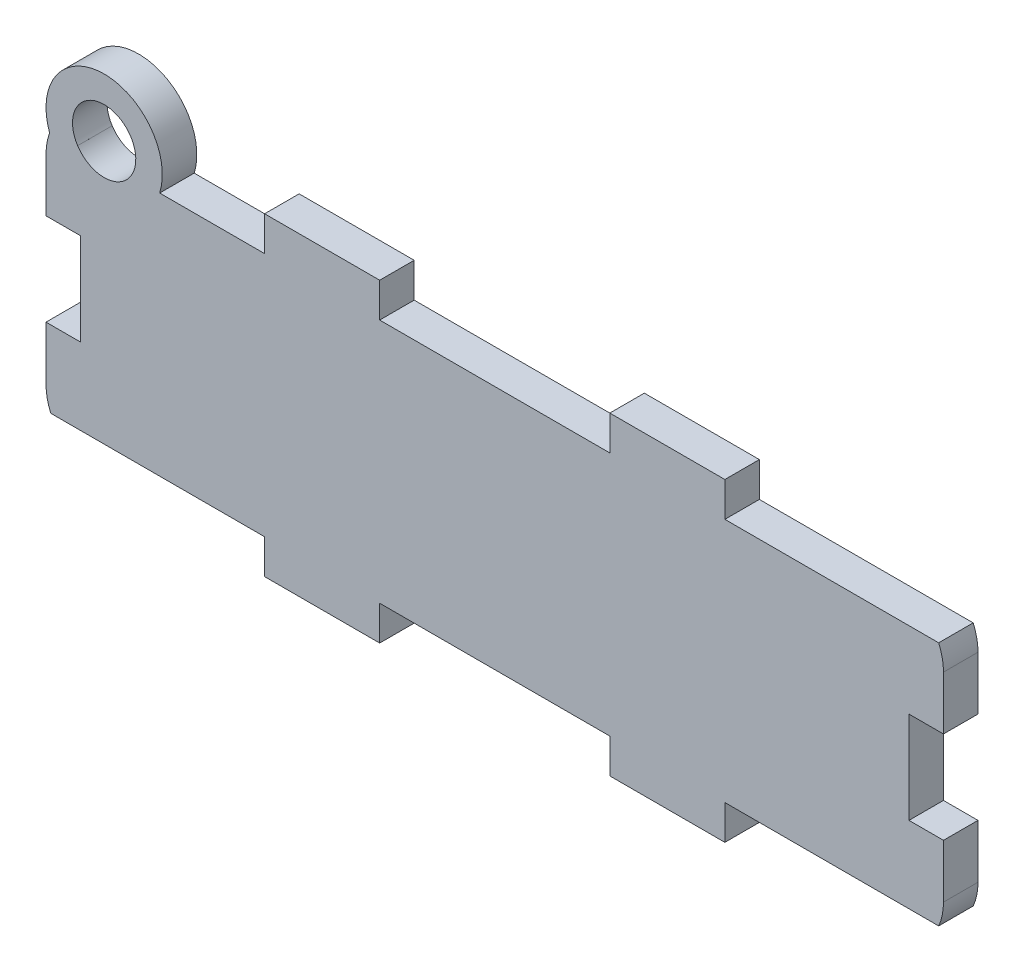
SolidWorks part; units mm, degrees
ref_plane "Front Plane" through (0, 0, 0) normal (0, 0, 1) x (1, 0, 0)
ref_plane "Top Plane" through (0, 0, 0) normal (0, 1, 0) x (1, 0, 0)
ref_plane "Right Plane" through (0, 0, 0) normal (1, 0, 0) x (0, 0, -1)
sketch "Sketch1" plane through (0, 0, 0) normal (0, 0, 1) x (1, 0, 0)
  line L0 (52, -3) -> (52, 0) construction
  line L1 (-7, -3) -> (3, -3)
  line L2 (-26, 2) -> (-26, 19.3118)
  line L3 (-7, 24.3118) -> (3, 24.3118)
  line L4 (52, 2) -> (52, 19.3118)
  line L5 (-26, -3) -> (52, 24.3118) construction
  line L6 (-26, 24.3118) -> (52, -3) construction
  line L7 (23, -3) -> (33, -3)
  line L8 (-7, 0) -> (-25.5826, 0)
  line L9 (-7, 0) -> (-7, -3)
  line L12 (-7, 0) -> (-26, -3) construction
  line L13 (-7, -3) -> (-26, 0) construction
  line L15 (3, -3) -> (3, 0)
  line L16 (3, 0) -> (23, 0)
  line L17 (23, -3) -> (23, 0)
  line L18 (3, -3) -> (23, 0) construction
  line L19 (3, 0) -> (23, -3) construction
  line L21 (33, -3) -> (33, 0)
  line L22 (33, 0) -> (51.5826, 0)
  line L24 (33, -3) -> (52, 0) construction
  line L25 (33, 0) -> (52, -3) construction
  line L27 (-33.6771, 10.6559) -> (59.6771, 10.6559) construction
  line L28 (33, 24.3118) -> (33, 21.3118)
  line L29 (23, 24.3118) -> (33, 24.3118)
  line L30 (23, 24.3118) -> (23, 21.3118)
  line L31 (3, 24.3118) -> (3, 21.3118)
  line L32 (-7, 21.3118) -> (-7, 24.3118)
  line L34 (-7, 21.3118) -> (-25.5826, 21.3118)
  line L35 (3, 21.3118) -> (23, 21.3118)
  line L36 (33, 21.3118) -> (51.5826, 21.3118)
  arc A1 (-26, 19.3118) -> (-25.5826, 21.3118) centre (-21, 19.3118) cw
  arc A2 (51.5826, 21.3118) -> (52, 19.3118) centre (47, 19.3118) cw
  arc A4 (-25.5826, 0) -> (-26, 2) centre (-21, 2) cw
  arc A5 (51.5826, 0) -> (52, 2) centre (47, 2) ccw
  point P4 (13, 10.6559)
  point P24 (-16.5, -1.5)
  point P29 (13, -1.5)
  point P35 (42.5, -1.5)
  point P41 (13, 10.6559)
extrude "Boss-Extrude1" add sketch "Sketch1" along normal blind 3
sketch "Sketch3" plane through (0, 0, 0) normal (0, 0, -1) x (-1, 0, 0)
  circle A0 centre (20.9461, 22.8118) radius 2.75 construction
  circle A1 centre (20.9461, 22.8118) radius 2.75
  arc A2 (25.6856, 21.057) -> (16.1199, 21.3118) centre (20.9461, 22.8118) ccw construction
  arc A3 (25.6856, 21.057) -> (16.1199, 21.3118) centre (20.9461, 22.8118) ccw construction
  circle A4 centre (20.9461, 22.8118) radius 5.0539
extrude "Boss-Extrude3" add sketch "Sketch3" against normal blind 3
sketch "Sketch4" plane through (0, 0, 0) normal (0, 0, -1) x (-1, 0, 0)
  line L0 (23.2507, 21.3118) -> (18.6415, 21.3118)
  arc A2 (18.6415, 21.3118) -> (23.2507, 21.3118) centre (20.9461, 22.8118) ccw
extrude "Cut-Extrude1" cut sketch "Sketch4" against normal blind 3
sketch "Sketch5" plane through (0, 0, 0) normal (0, 0, -1) x (-1, 0, 0)
  line L0 (26, 10.6559) -> (-52, 10.6559) construction
  line L1 (26, 19.3118) -> (26, 2) construction
  line L2 (-52, 2) -> (-52, 19.3118) construction
  line L3 (-13, 0) -> (-13, 21.3118) construction
  line L4 (26, 6.6559) -> (23, 6.6559)
  line L5 (26, 6.6559) -> (26, 14.6559)
  line L6 (26, 14.6559) -> (23, 14.6559)
  line L7 (23, 6.6559) -> (23, 14.6559)
  line L8 (26, 6.6559) -> (23, 14.6559) construction
  line L9 (26, 14.6559) -> (23, 6.6559) construction
  line L10 (-3, 0) -> (-23, 0) construction
  line L11 (-23, 21.3118) -> (-3, 21.3118) construction
  line L12 (-52, 14.6559) -> (-49, 6.6559) construction
  line L13 (-52, 6.6559) -> (-49, 14.6559) construction
  line L14 (-49, 6.6559) -> (-49, 14.6559)
  line L15 (-52, 14.6559) -> (-49, 14.6559)
  line L16 (-52, 6.6559) -> (-52, 14.6559)
  line L17 (-52, 6.6559) -> (-49, 6.6559)
  point P10 (24.5, 10.6559)
  point P21 (-50.5, 10.6559)
  dimension "D1" = 3
  dimension "D2" = 8
extrude "Cut-Extrude2" cut sketch "Sketch5" against normal blind 3
